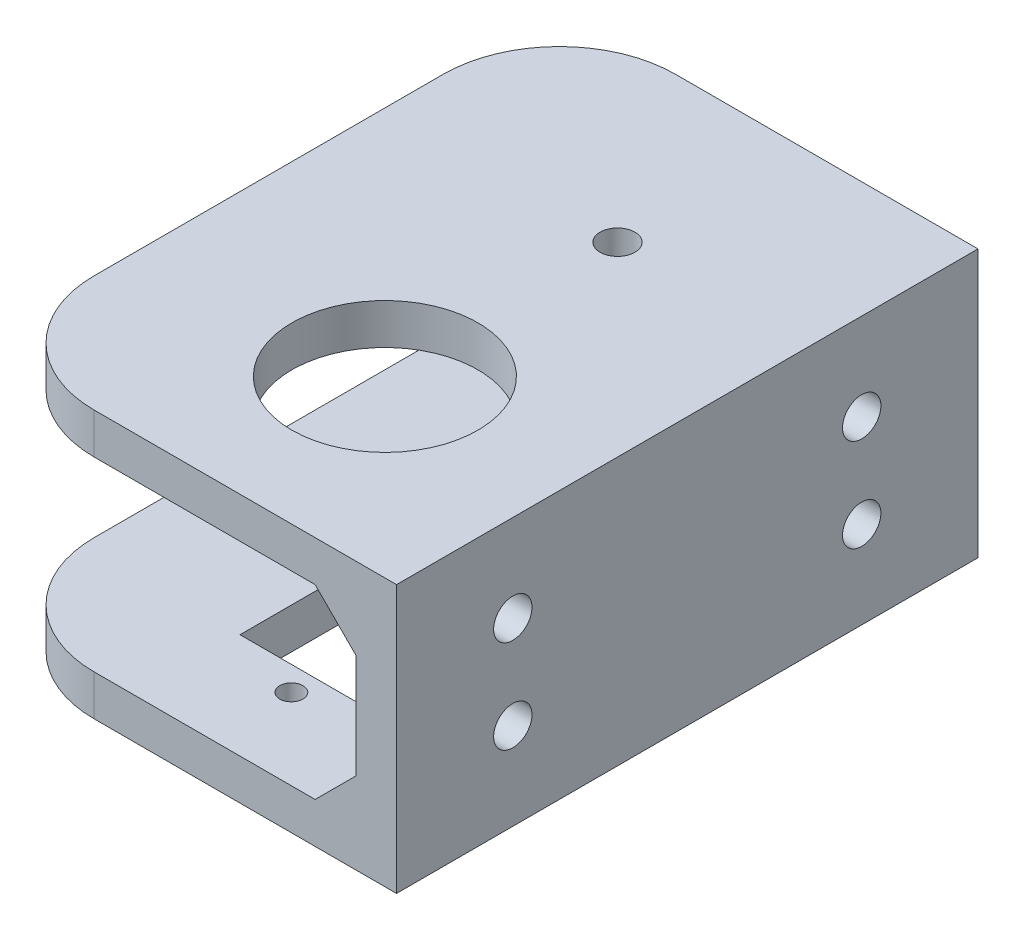
SolidWorks part; units mm, degrees
ref_plane "前视基准面" through (0, 0, 0) normal (0, 0, 1) x (1, 0, 0)
ref_plane "上视基准面" through (0, 0, 0) normal (0, 1, 0) x (1, 0, 0)
ref_plane "右视基准面" through (0, 0, 0) normal (1, 0, 0) x (0, 0, -1)
sketch "草图1" plane through (0, 0, 0) normal (0, 0, 1) x (1, 0, 0)
  line L0 (-45, 11.5) -> (0, 11.5)
  line L1 (0, 11.5) -> (0, -11.5)
  line L2 (0, -11.5) -> (-45, -11.5)
  line L3 (-45, 8) -> (-3.5, 8)
  line L4 (-3.5, 8) -> (-3.5, -8)
  line L5 (-3.5, -8) -> (-45, -8)
  line L6 (-45, 11.5) -> (-45, 8)
  line L7 (-45, -8) -> (-45, -11.5)
  dimension "D1" = 3.5
  dimension "D2" = 23
  dimension "D3" = 45
extrude "凸台-拉伸1" add sketch "草图1" along normal blind 50
sketch "草图2" plane through (0, -11.5, 0) normal (0, -1, 0) x (1, 0, 0)
  line L0 (0, 50) -> (0, 0) construction
  line L1 (-16, 25) -> (-40.6813, 25) construction
  line L2 (-16, 35) -> (-16, 50) construction
  line L3 (-45, 50) -> (0, 50) construction
  line L4 (-16, 15) -> (-16, 0) construction
  line L5 (-45, 0) -> (0, 0) construction
  circle A0 centre (-16, 35) radius 10 construction
  circle A1 centre (-16, 15) radius 10 construction
  circle A2 centre (-16, 35) radius 1.5
  circle A3 centre (-16, 15) radius 1.5
  dimension "D1" = 20
  dimension "D3" = 3
  dimension "D2" = 16
extrude "切除-拉伸1" cut sketch "草图2" against normal blind 70 from surface at -19.5 starting at face at (-24.25, 8, 25)
sketch "草图3" plane through (0, -11.5, 0) normal (0, -1, 0) x (1, 0, 0)
  line L2 (-36, 10) -> (-36, 40)
  line L6 (-40.6813, 25) -> (-23.9708, 25) construction
  line L7 (-26, 0) -> (0, 0)
  line L8 (0, 0) -> (0, 50)
  line L9 (0, 50) -> (-26, 50)
  arc A0 (-36, 40) -> (-26, 50) centre (-26, 40) cw
  arc A1 (-26, 0) -> (-36, 10) centre (-26, 10) cw
  dimension "D1" = 10
  dimension "D2" = 10
extrude "切除-拉伸2" cut sketch "草图3" against normal blind 70 flip side to cut
sketch "草图4" plane through (0, 11.5, 0) normal (0, 1, 0) x (1, 0, 0)
  line L0 (-16, -15.375) -> (-16, -43.045) construction
  circle A0 centre (-16, -35) radius 1.5 construction
  circle A1 centre (-16, -35) radius 1.5 construction
  dimension "D1" = 19.625
  dimension "D2" = 8.045
sketch "草图5" plane through (0, -11.5, 0) normal (0, -1, 0) x (1, 0, 0)
  line L0 (-16, 15.375) -> (-16, 43.045) construction
  line L1 (-16, 15.375) -> (-16, 43.045) construction
  circle A0 centre (-16, 43.045) radius 1
  circle A1 centre (-16, 15.375) radius 1
  dimension "D1" = 2
extrude "切除-拉伸5" cut sketch "草图5" against normal blind 10
sketch "草图6" plane through (0, -11.5, 0) normal (0, -1, 0) x (1, 0, 0)
  line L0 (-16, 15.375) -> (-16, 43.045) construction
  line L2 (-9.5, 17.46) -> (-22.5, 17.46)
  line L3 (-9.5, 17.46) -> (-9.5, 40.96)
  line L4 (-9.5, 40.96) -> (-22.5, 40.96)
  line L5 (-22.5, 17.46) -> (-22.5, 40.96)
  line L6 (-9.5, 17.46) -> (-22.5, 40.96) construction
  line L7 (-9.5, 40.96) -> (-22.5, 17.46) construction
  circle A0 centre (-16, 43.045) radius 1 construction
  circle A1 centre (-16, 43.045) radius 1 construction
  circle A2 centre (-16, 15.375) radius 1 construction
  circle A3 centre (-16, 15.375) radius 1 construction
  point P6 (-16, 29.21)
  dimension "D1" = 23.5
  dimension "D2" = 13
extrude "切除-拉伸6" cut sketch "草图6" against normal blind 10
sketch "草图7" plane through (0, 0, 0) normal (1, 0, 0) x (0, 0, -1)
  line L0 (0, 0) -> (-54.0378, 0) construction
  line L1 (-50, -11.5) -> (-50, 11.5) construction
  line L2 (0, -11.5) -> (0, 11.5) construction
  circle A0 centre (-10, 4) radius 1.65
  circle A1 centre (-40, 4) radius 1.65
  circle A2 centre (-10, -4) radius 1.65
  circle A3 centre (-40, -4) radius 1.65
  dimension "D1" = 3.3
  dimension "D2" = 10
  dimension "D3" = 10
  dimension "D4" = 4
extrude "切除-拉伸7" cut sketch "草图7" against normal blind 10
sketch "草图8" plane through (0, 11.5, 0) normal (0, 1, 0) x (1, 0, 0)
  circle A0 centre (-16, -35) radius 1.5 construction
  circle A1 centre (-16, -35) radius 1.5 construction
  circle A2 centre (-16, -35) radius 8
extrude "切除-拉伸8" cut sketch "草图8" against normal blind 10
sketch "草图9" plane through (0, 0, 0) normal (0, 0, -1) x (-1, 0, 0)
  line L0 (3.5, 8) -> (3.5, -8) construction
  line L1 (26, 8) -> (3.5, 8) construction
  line L2 (3.5, 4.5) -> (3.5, 8)
  line L3 (3.5, 8) -> (7, 8)
  line L4 (7, 8) -> (3.5, 4.5)
  line L5 (0, 0) -> (3.5, 0) construction
  line L6 (0, -11.5) -> (0, 11.5) construction
  line L7 (3.5, -8) -> (7, -8)
  line L8 (3.5, -4.5) -> (3.5, -8)
  line L9 (7, -8) -> (3.5, -4.5)
  point P1 (7, 8)
  point P2 (3.5, 4.5)
  dimension "D1" = 3.5
  dimension "D2" = 3.5
extrude "凸台-拉伸2" add sketch "草图9" against normal blind 3.5
sketch "草图10" plane through (0, 0, 50) normal (0, 0, 1) x (1, 0, 0)
  line L0 (0, 0) -> (-3.5, 0) construction
  line L1 (-3.5, 8) -> (-3.5, -8) construction
  line L2 (-3.5, 8) -> (-7, 8)
  line L3 (-7, 8) -> (-3.5, 4.5)
  line L4 (-3.5, 4.5) -> (-3.5, 8)
  line L5 (-3.5, -8) -> (-3.5, -4.5)
  line L6 (-3.5, -4.5) -> (-7, -8)
  line L7 (-7, -8) -> (-3.5, -8)
extrude "凸台-拉伸3" add sketch "草图10" against normal blind 3.5
